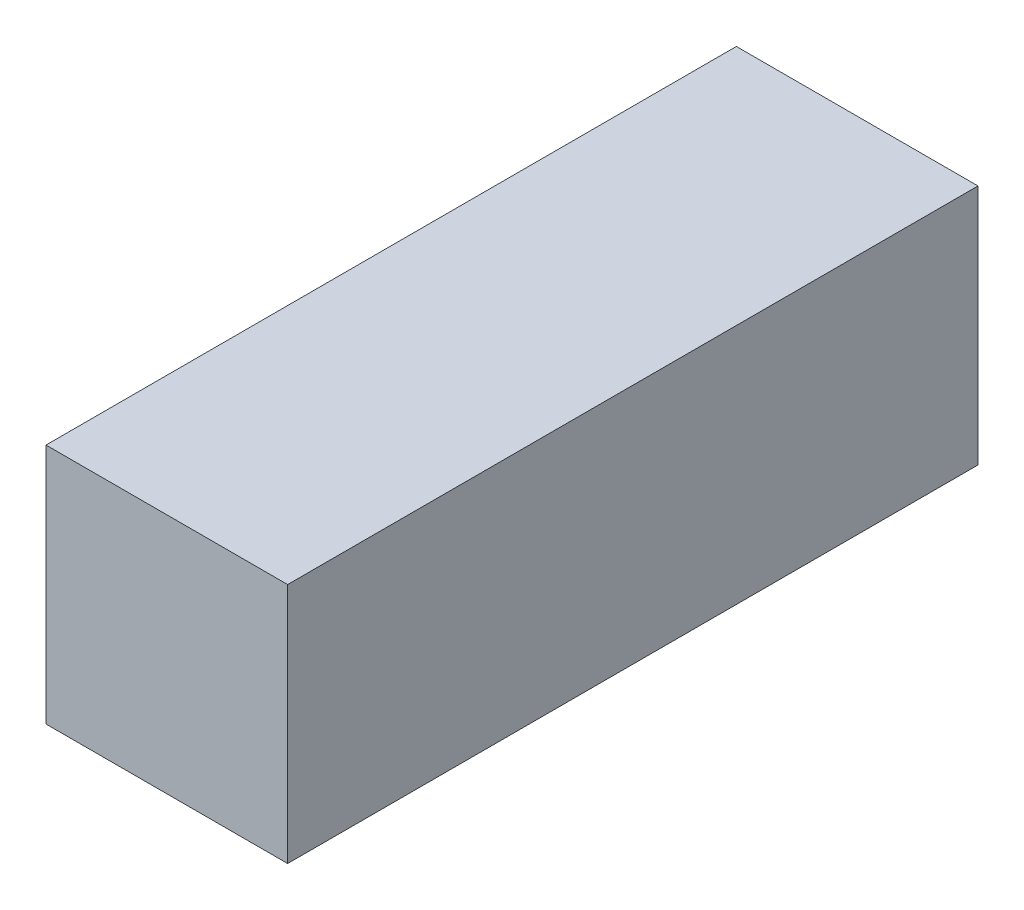
SolidWorks part; units mm, degrees
ref_plane "Front Plane" through (0, 0, 0) normal (0, 0, 1) x (1, 0, 0)
ref_plane "Top Plane" through (0, 0, 0) normal (0, 1, 0) x (1, 0, 0)
ref_plane "Right Plane" through (0, 0, 0) normal (1, 0, 0) x (0, 0, -1)
sketch "Sketch1" plane through (0, 0, 0) normal (0, 0, 1) x (1, 0, 0)
  line L1 (0, 0) -> (7, 0)
  line L2 (0, 0) -> (0, 7)
  line L3 (0, 7) -> (7, 7)
  line L4 (7, 0) -> (7, 7)
extrude "Boss-Extrude1" add sketch "Sketch1" along normal blind 20
